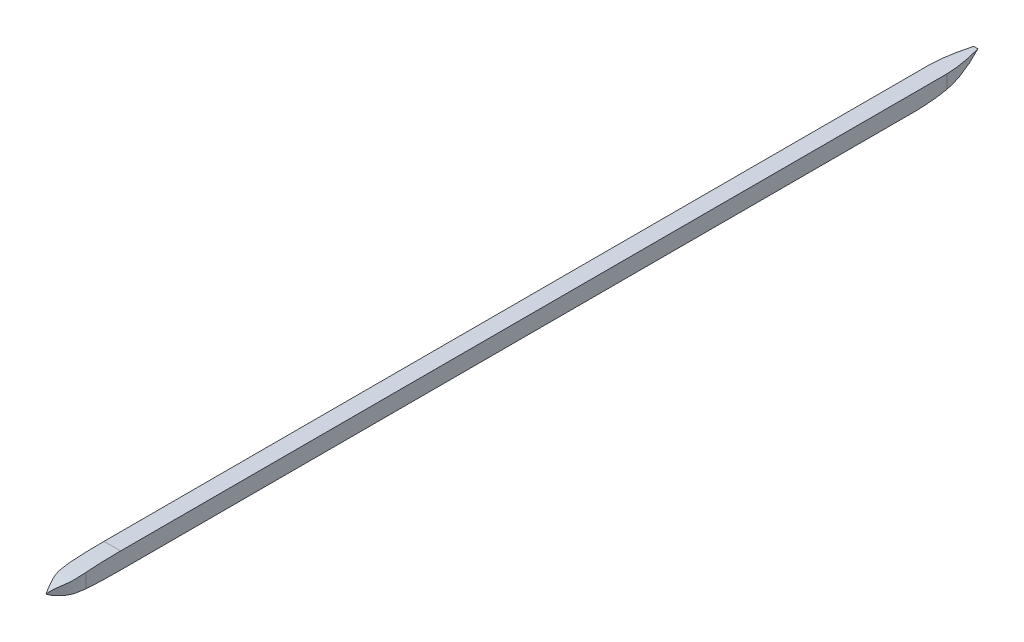
SolidWorks part; units mm, degrees
ref_plane "Front Plane" through (0, 0, 0) normal (0, 0, 1) x (1, 0, 0)
ref_plane "Top Plane" through (0, 0, 0) normal (0, 1, 0) x (1, 0, 0)
ref_plane "Right Plane" through (0, 0, 0) normal (1, 0, 0) x (0, 0, -1)
sketch "Sketch2" plane through (0, 0, 0) normal (1, 0, 0) x (0, 0, -1)
  line L1 (355.6, 6.35) -> (-355.6, 6.35)
  line L2 (355.6, 6.35) -> (355.6, -6.35)
  line L3 (355.6, -6.35) -> (-355.6, -6.35)
  line L4 (-355.6, 6.35) -> (-355.6, -6.35)
  line L5 (355.6, 6.35) -> (-355.6, -6.35) construction
  line L6 (355.6, -6.35) -> (-355.6, 6.35) construction
  point P0 (0, 0)
  dimension "D1" = 711.2
  dimension "D2" = 12.7
extrude "Boss-Extrude2" add sketch "Sketch2" along normal mid plane 12.7
sketch "Sketch4" plane through (6.35, 0, 0) normal (1, 0, 0) x (0, 0, -1)
  line L0 (-355.6, 0) -> (-304.8741, 0) construction
  line L1 (-355.6, 6.35) -> (-355.6, -6.35) construction
  line L2 (355.6, 6.35) -> (-355.6, 6.35) construction
  line L3 (-267.773, 6.35) -> (-341.9751, 6.35) construction
  line L4 (-355.6, -6.35) -> (355.6, -6.35) construction
  line L5 (-284.4258, -6.35) -> (-325.3233, -6.35) construction
  line L6 (-304.8741, 6.35) -> (-304.8741, 13.8655)
  line L7 (-304.8741, 13.8655) -> (-363.5123, 13.8655)
  line L8 (-363.5123, 13.8655) -> (-363.5123, -12.3283)
  line L9 (-363.5123, -12.3283) -> (-304.8746, -12.3283)
  line L10 (-304.8746, -12.3283) -> (-304.8746, -6.35)
  spline S0 degree 2 poles (-355.6, 0) (-345.5912, 6.35) (-304.8741, 6.35) knots 0 0 0 1 1 1
  spline S1 degree 2 poles (-355.6, 0) (-348.0973, -6.35) (-304.8746, -6.35) knots 0 0 0 1 1 1
extrude "Cut-Extrude1" cut sketch "Sketch4" against normal through all
sketch "Sketch5" plane through (0, 6.35, 0) normal (0, 1, 0) x (1, 0, 0)
  line L0 (0, -355.6) -> (0, -304.8741) construction
  line L1 (-6.35, -355.6) -> (6.35, -355.6) construction
  line L2 (-6.35, -304.8741) -> (6.35, -304.8741) construction
  line L3 (-6.35, -337.5702) -> (-6.35, -272.1773) construction
  line L4 (-6.35, -304.8741) -> (-23.9889, -304.8741)
  line L5 (-23.9889, -304.8741) -> (-23.9889, -362.654)
  line L6 (-23.9889, -362.654) -> (16.904, -362.654)
  line L7 (16.904, -362.654) -> (16.904, -304.8741)
  line L8 (16.904, -304.8741) -> (6.35, -304.8741)
  spline S0 degree 3 poles (-6.35, -304.8741) (-6.35, -345.7446) (-7.3263, -338.5962) (0, -355.6) knots 0 0 0 0 1 1 1 1
  spline S1 degree 3 poles (6.35, -304.8741) (6.35, -345.7446) (7.3263, -338.5962) (0, -355.6) knots 0 0 0 0 1 1 1 1
extrude "Cut-Extrude2" cut sketch "Sketch5" against normal through all
sketch "Sketch6" plane through (6.35, 0, 0) normal (1, 0, 0) x (0, 0, -1)
  line L0 (-304.8746, -6.35) -> (355.6, -6.35) construction
  line L1 (286.8487, -6.35) -> (286.8487, -20.4744)
  line L2 (286.8487, -20.4744) -> (367.423, -20.4744)
  line L3 (367.423, -20.4744) -> (367.423, 6.35)
  line L4 (367.423, 6.35) -> (355.6, 6.35)
  spline S0 degree 3 poles (355.6, 6.35) (329.9903, -6.5637) (313.3238, -6.629) (286.8487, -6.35) knots 0 0 0 0 1 1 1 1
extrude "Cut-Extrude3" cut sketch "Sketch6" against normal through all
sketch "Sketch7" plane through (0, 6.35, 0) normal (0, 1, 0) x (1, 0, 0)
  line L0 (0, 355.6) -> (0, 310.1123) construction
  line L1 (6.35, 355.6) -> (-6.35, 355.6) construction
  line L2 (1.651, 355.6) -> (-1.651, 355.6)
  line L3 (-6.35, 355.6) -> (-6.35, -304.8741) construction
  line L4 (-6.35, 292.621) -> (-6.35, 327.6064) construction
  line L5 (-6.35, 310.1137) -> (-23.6205, 310.1137)
  line L6 (-23.6205, 310.1137) -> (-23.6205, 363.5519)
  line L7 (-23.6205, 363.5519) -> (18.9258, 363.5519)
  line L8 (18.9258, 363.5519) -> (18.9258, 310.1137)
  line L9 (18.9258, 310.1137) -> (6.35, 310.1137)
  spline S0 degree 3 poles (-1.651, 355.6) (-7.5431, 333.6078) (-6.35, 324.691) (-6.35, 310.1137) knots 0 0 0 0 1 1 1 1
  spline S1 degree 3 poles (1.651, 355.6) (7.5431, 333.6078) (6.35, 324.691) (6.35, 310.1137) knots 0 0 0 0 1 1 1 1
  point P8 (0, 355.6)
  dimension "D1" = 3.302
extrude "Cut-Extrude4" cut sketch "Sketch7" against normal through all
